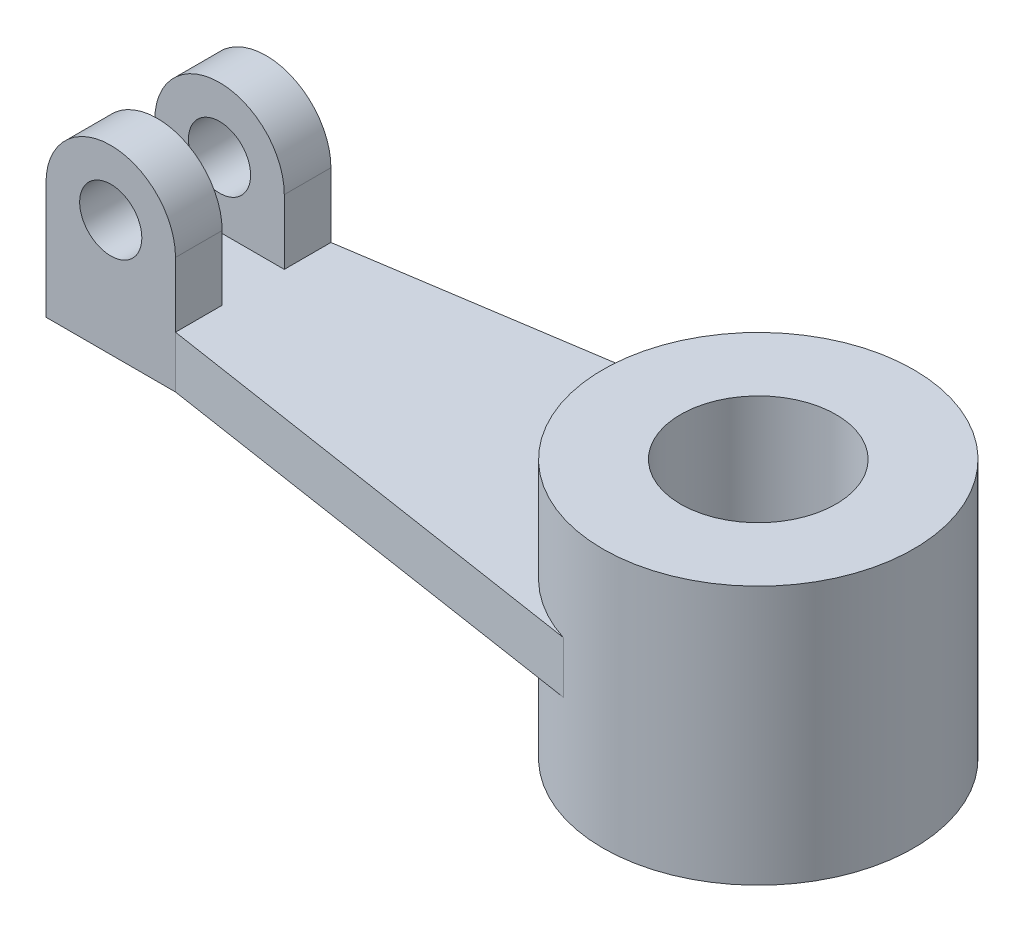
SolidWorks part; units mm, degrees
ref_plane "Front Plane" through (0, 0, 0) normal (0, 0, 1) x (1, 0, 0)
ref_plane "Top Plane" through (0, 0, 0) normal (0, 1, 0) x (1, 0, 0)
ref_plane "Right Plane" through (0, 0, 0) normal (1, 0, 0) x (0, 0, -1)
sketch "Sketch1" plane through (0, 0, 0) normal (0, 1, 0) x (1, 0, 0)
  circle A0 centre (0, 0) radius 30
  circle A1 centre (0, 0) radius 15
  dimension "D1" = 60
  dimension "D2" = 30
extrude "Boss-Extrude2" add sketch "Sketch1" along normal mid plane 50
sketch "Sketch3" plane through (0, 0, 0) normal (0, 1, 0) x (1, 0, 0)
  line L0 (0, 60.199) -> (0, -73.8535) construction
  line L1 (-170.7114, 0) -> (106.7104, 0) construction
  line L3 (-122.5, 15) -> (-122.5, -15)
  line L4 (-122.5, 15) -> (-97.5, 15)
  line L5 (-122.5, -15) -> (-97.5, -15)
  line L6 (-97.5, 15) -> (0, 30)
  line L7 (-97.5, -15) -> (0, -30)
  circle A0 centre (0, 0) radius 30 construction
  circle A3 centre (0, 0) radius 30
  arc A4 (0, 30) -> (0, -30) centre (0, 0) ccw
  dimension "D3" = 0
  dimension "D1" = 30
  dimension "D2" = 25
extrude "Boss-Extrude3" add sketch "Sketch3" along normal mid plane 10 contours A4 L6 L4 L3 L5 L7
sketch "Sketch4" plane through (0, 0, 15) normal (0, 0, 1) x (1, 0, 0)
  line L0 (-122.5, 5) -> (-122.5, 17.5)
  line L1 (-97.5, 5) -> (-97.5, 17.5)
  line L2 (-97.5, 5) -> (-97.5, -5) construction
  line L3 (-122.5, 5) -> (-122.5, -5) construction
  line L8 (-122.5, -5) -> (-97.5, -5)
  line L9 (-97.5, -5) -> (-97.5, 5)
  line L10 (-97.5, 5) -> (-122.5, 5)
  line L11 (-122.5, 5) -> (-122.5, -5)
  line L12 (-122.5, -5) -> (-97.5, -5)
  line L13 (-97.5, -5) -> (-97.5, 5)
  line L15 (-122.5, 5) -> (-122.5, -5)
  arc A0 (-122.5, 17.5) -> (-97.5, 17.5) centre (-110, 17.5) cw
  dimension "D2" = 12.5
  dimension "D1" = 12.5
  dimension "D3" = 0
extrude "Boss-Extrude5" add sketch "Sketch4" against normal blind 9
sketch "Sketch6" plane through (0, 0, -15) normal (0, 0, -1) x (-1, 0, 0)
  line L0 (97.5, 5) -> (97.5, 17.5)
  line L1 (122.5, 5) -> (122.5, 17.5)
  line L6 (97.5, -5) -> (122.5, -5)
  line L7 (122.5, -5) -> (122.5, 5)
  line L8 (122.5, 5) -> (97.5, 5)
  line L9 (97.5, 5) -> (97.5, -5)
  line L10 (97.5, -5) -> (122.5, -5)
  line L11 (122.5, -5) -> (122.5, 5)
  line L13 (97.5, 5) -> (97.5, -5)
  arc A0 (97.5, 17.5) -> (122.5, 17.5) centre (110, 17.5) cw
  circle A1 centre (110, 17.5) radius 6
  dimension "D1" = 0
extrude "Boss-Extrude6" add sketch "Sketch6" against normal blind 9
sketch "Sketch7" plane through (0, 0, 15) normal (0, 0, 1) x (1, 0, 0)
  line L0 (-110, 41.9675) -> (-110, -19.9661) construction
  line L1 (-132.3363, 17.5) -> (-86.5945, 17.5) construction
  circle A0 centre (-110, 17.5) radius 6
  dimension "D1" = 12
extrude "Cut-Extrude2" cut sketch "Sketch7" against normal through all
